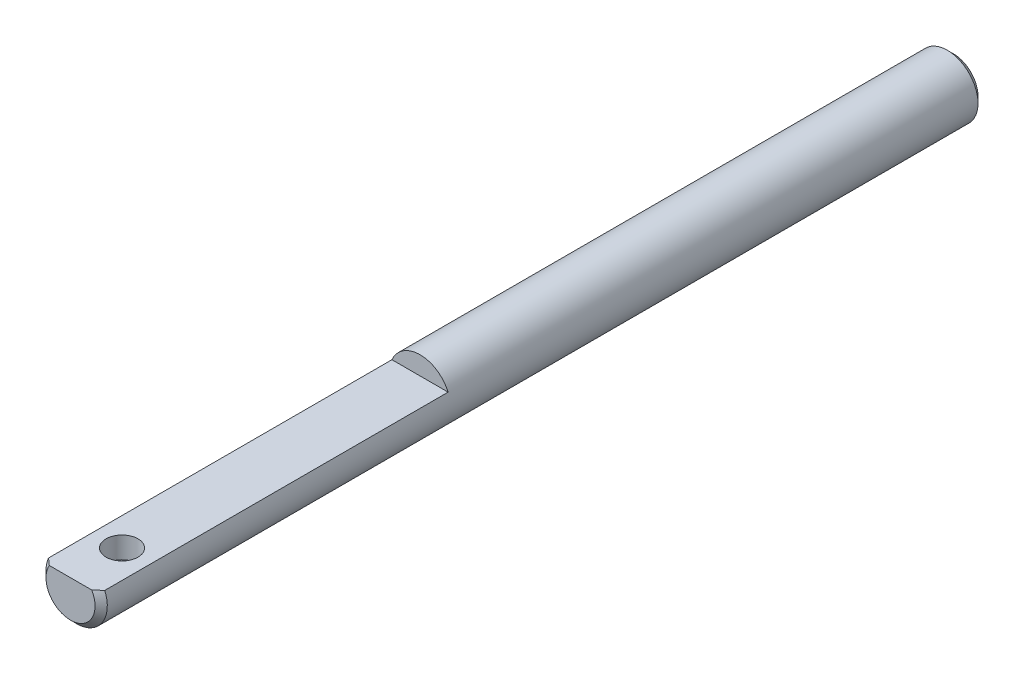
SolidWorks part; units mm, degrees
material "Alloy Steel"
ref_plane "Front" through (0, 0, 0) normal (0, 0, 1) x (1, 0, 0)
ref_plane "Top" through (0, 0, 0) normal (0, 1, 0) x (1, 0, 0)
ref_plane "Right" through (0, 0, 0) normal (1, 0, 0) x (0, 0, -1)
sketch "Sketch1" plane through (0, 0, 0) normal (0, 0, 1) x (1, 0, 0)
  circle A0 centre (0, 0) radius 3.175
  dimension "D1" = 6.35
extrude "Extrude1" add sketch "Sketch1" along normal mid plane 91.44
chamfer "Chamfer1" distance 0.635 angle 45 2 edges at (3.175, 0, -45.72) (3.175, 0, 45.72)
ref_plane "Plane1" through (0, 0, 9.525) normal (0, 0, 1) x (1, 0, 0)
sketch "Sketch13" plane through (0, 0, 9.525) normal (0, 0, 1) x (1, 0, 0)
  line L0 (0, -3.175) -> (7.1257, -3.175) construction
  line L3 (-2.9099, 1.27) -> (2.9099, 1.27)
  circle A0 centre (0, 0) radius 3.175 construction
  arc A1 (2.9099, 1.27) -> (-2.9099, 1.27) centre (0, 0) ccw
  dimension "D1" = 1.27
  dimension "D2" = 4.445
extrude "Extrude7" cut sketch "Sketch13" along normal through all
sketch "Sketch14" plane through (0, 1.27, 0) normal (0, 1, 0) x (1, 0, 0)
  line L2 (-3.175, 45.085) -> (-3.175, -45.085) construction
  line L4 (-2.54, -45.72) -> (2.54, -45.72) construction
  circle A0 centre (0, -40.386) radius 1.651
  dimension "D1" = 3.302
  dimension "D3" = 3.175
  dimension "D2" = 5.334
extrude "Cut-Extrude1" cut sketch "Sketch14" against normal blind 2.2225
equation "\"D1@Chamfer1\" = \"D1@Sketch1\" * .1"
